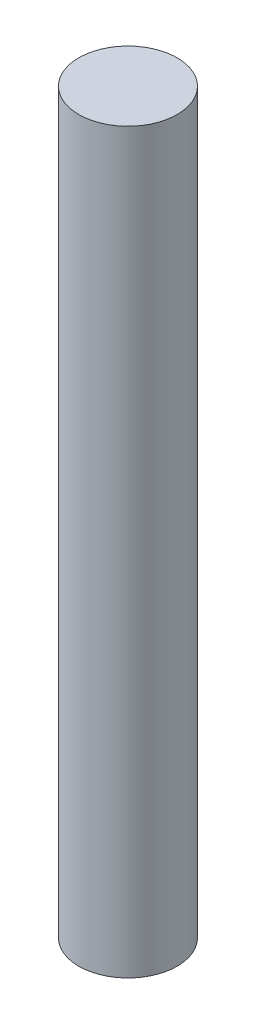
SolidWorks part; units mm, degrees
ref_plane "Front Plane" through (0, 0, 0) normal (0, 0, 1) x (1, 0, 0)
ref_plane "Top Plane" through (0, 0, 0) normal (0, 1, 0) x (1, 0, 0)
ref_plane "Right Plane" through (0, 0, 0) normal (1, 0, 0) x (0, 0, -1)
sketch "Sketch1" plane through (0, 0, 0) normal (0, 1, 0) x (1, 0, 0)
  circle A0 centre (0, 0) radius 6.35
  dimension "D1" = 12.7
extrude "Boss-Extrude1" add sketch "Sketch1" along normal blind 95.25
